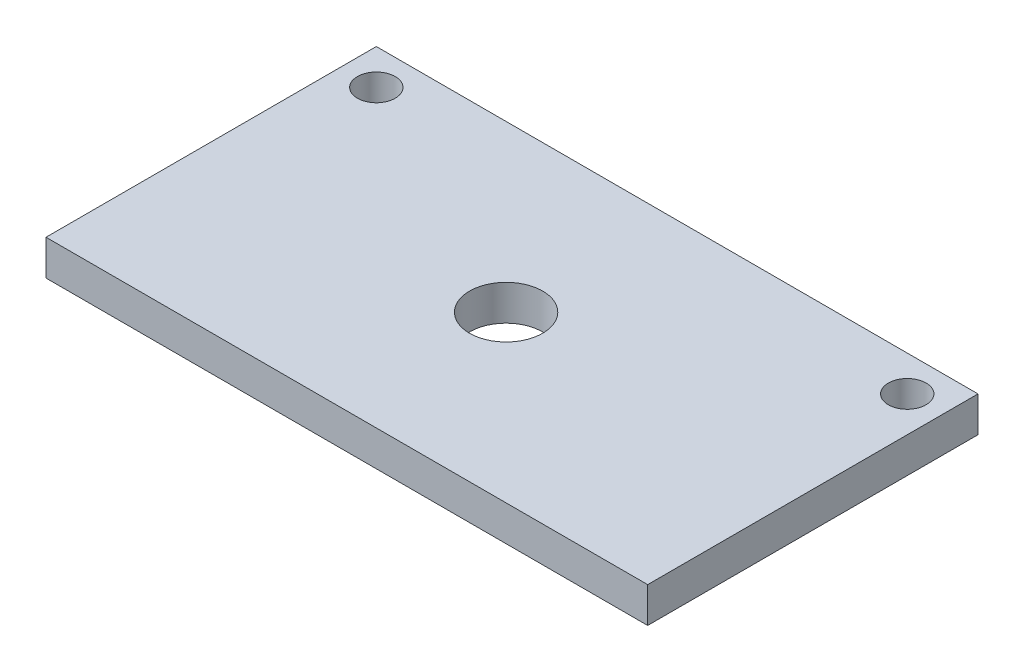
SolidWorks part; units mm, degrees
ref_plane "Front Plane" through (0, 0, 0) normal (0, 0, 1) x (1, 0, 0)
ref_plane "Top Plane" through (0, 0, 0) normal (0, 1, 0) x (1, 0, 0)
ref_plane "Right Plane" through (0, 0, 0) normal (1, 0, 0) x (0, 0, -1)
sketch "Sketch1" plane through (0, 0, 0) normal (0, 1, 0) x (1, 0, 0)
  line L1 (-26.5823, 14.2405) -> (24.4177, 14.2405)
  line L2 (-26.5823, 14.2405) -> (-26.5823, -13.7595)
  line L3 (-26.5823, -13.7595) -> (24.4177, -13.7595)
  line L4 (24.4177, 14.2405) -> (24.4177, -13.7595)
  dimension "D1" = 51
  dimension "D2" = 28
extrude "Boss-Extrude1" add sketch "Sketch1" along normal blind 3
sketch "Sketch2" plane through (0, 3, 0) normal (0, 1, 0) x (1, 0, 0)
  line L0 (24.4177, -13.7595) -> (24.4177, 14.2405) construction
  line L1 (24.4177, 14.2405) -> (-26.5823, 14.2405) construction
  line L2 (-26.5823, 14.2405) -> (-26.5823, -13.7595) construction
  circle A0 centre (-23.5823, 11.2405) radius 1.6
  circle A1 centre (21.4177, 11.2405) radius 1.6
  dimension "D1" = 3
  dimension "D2" = 3
  dimension "D3" = 3
  dimension "D4" = 3
  dimension "D5" = 3
extrude "Cut-Extrude1" cut sketch "Sketch2" against normal blind 3
sketch "Sketch3" plane through (0, 3, 0) normal (0, 1, 0) x (1, 0, 0)
  line L0 (24.4177, 14.2405) -> (-26.5823, 14.2405) construction
  line L1 (-26.5823, 14.2405) -> (-26.5823, -13.7595) construction
  circle A0 centre (-1.5823, 0.2405) radius 3.1
  dimension "D1" = 14
  dimension "D2" = 25
extrude "Cut-Extrude2" cut sketch "Sketch3" against normal blind 3
